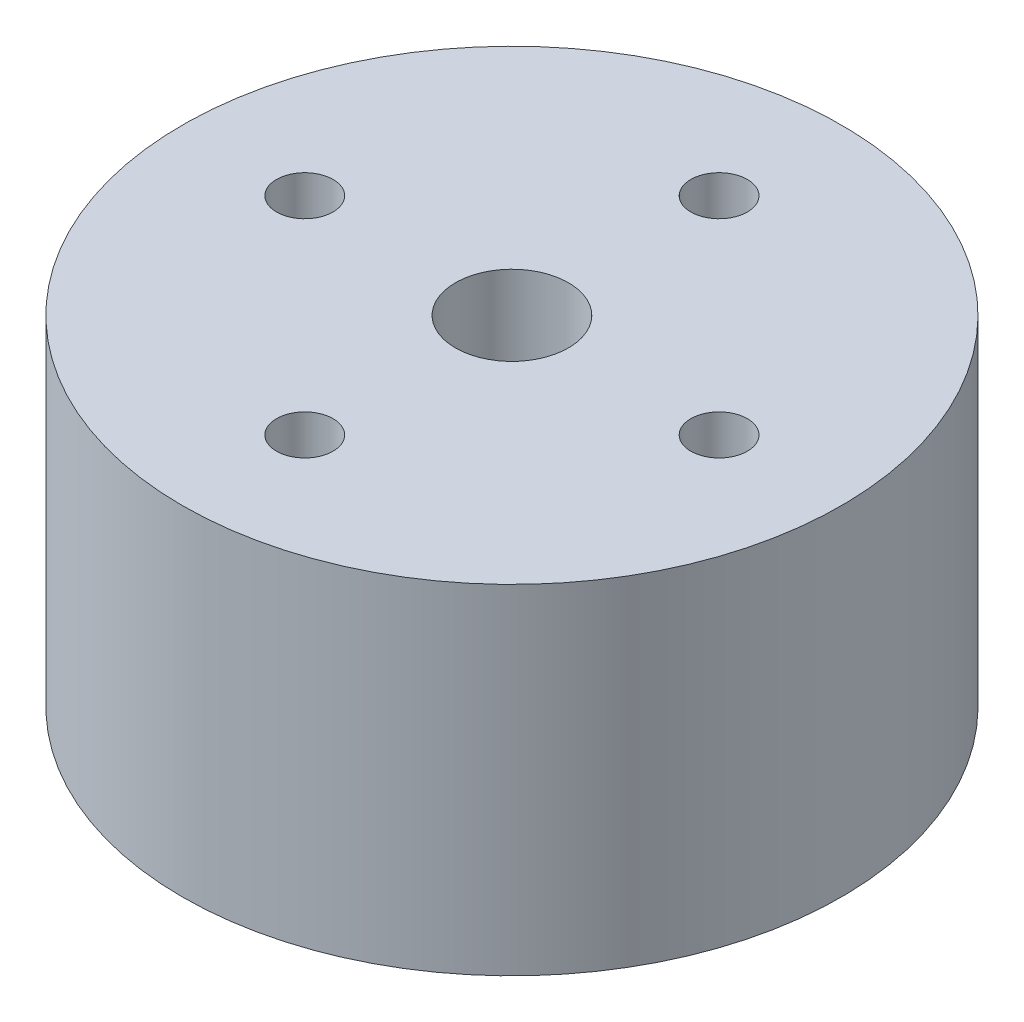
SolidWorks part; units mm, degrees
material "1060 Alloy"
ref_plane "Front Plane" through (0, 0, 0) normal (0, 0, 1) x (1, 0, 0)
ref_plane "Top Plane" through (0, 0, 0) normal (0, 1, 0) x (1, 0, 0)
ref_plane "Right Plane" through (0, 0, 0) normal (1, 0, 0) x (0, 0, -1)
sketch "Sketch1" plane through (0, 0, 0) normal (0, 1, 0) x (1, 0, 0)
  line L0 (-17.5, 0) -> (17.5, 0) construction
  line L1 (0, 0) -> (12.3744, 12.3744) construction
  circle A0 centre (0, 0) radius 17.5
  circle A1 centre (0, 0) radius 3
  circle A2 centre (0, 11) radius 1.5
  circle A3 centre (0, -11) radius 1.5
  circle A4 centre (11, 0) radius 1.5
  circle A5 centre (-11, 0) radius 1.5
  dimension "D1" = 35
  dimension "D2" = 6
  dimension "D3" = 3
  dimension "D4" = 11
  dimension "D5" = 45
extrude "Boss-Extrude1" add sketch "Sketch1" along normal blind 18
